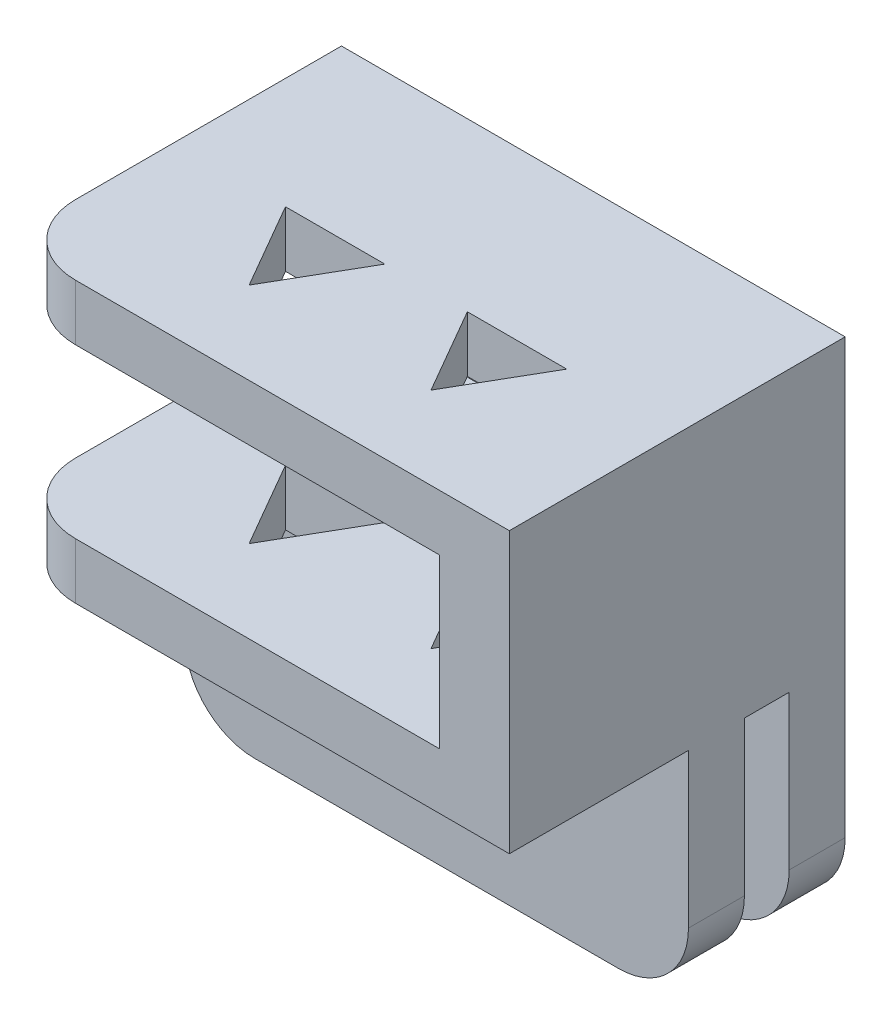
SolidWorks part; units mm, degrees
material "ABS"
ref_plane "Front Plane" through (0, 0, 0) normal (0, 0, 1) x (1, 0, 0)
ref_plane "Top Plane" through (0, 0, 0) normal (0, 1, 0) x (1, 0, 0)
ref_plane "Right Plane" through (0, 0, 0) normal (1, 0, 0) x (0, 0, -1)
sketch "Sketch1" plane through (0, 0, 0) normal (1, 0, 0) x (0, 0, -1)
  line L0 (6, -5) -> (6, -13)
  line L1 (-6, 5) -> (6, 5)
  line L2 (-6, 5) -> (-6, -5)
  line L3 (-6, -5) -> (0.4, -5)
  line L4 (6, 5) -> (6, -5)
  line L5 (-6, 5) -> (6, -5) construction
  line L6 (-6, -5) -> (6, 5) construction
  line L7 (6, -13) -> (4, -13)
  line L8 (4, -13) -> (4, -5)
  line L9 (2.4, -5) -> (2.4, -13)
  line L10 (2.4, -13) -> (0.4, -13)
  line L11 (0.4, -13) -> (0.4, -5)
  line L12 (2.4, -5) -> (4, -5)
  line L13 (0.4, -5) -> (2.4, -5) construction
  line L14 (4, -5) -> (6, -5) construction
  point P0 (0, 0)
  dimension "D1" = 2
  dimension "D2" = 2
  dimension "D3" = 8
  dimension "D4" = 8
  dimension "D5" = 1.6
  dimension "D6" = 10
  dimension "D7" = 12
extrude "Boss-Extrude1" add sketch "Sketch1" along normal mid plane 18
sketch "Sketch2" plane through (0, 0, 6) normal (0, 0, 1) x (1, 0, 0)
  line L0 (-6.5, 3) -> (-9, 3)
  line L1 (-6.5, 3) -> (6.5, 3)
  line L2 (-6.5, 3) -> (-6.5, -3) construction
  line L3 (-6.5, -3) -> (6.5, -3)
  line L4 (6.5, 3) -> (6.5, -3)
  line L5 (-6.5, 3) -> (6.5, -3) construction
  line L6 (-6.5, -3) -> (6.5, 3) construction
  line L7 (-9, 5) -> (-9, -5) construction
  line L8 (-6.5, -3) -> (-9, -3)
  line L9 (-9, 3) -> (-9, -3)
  point P0 (0, 0)
  dimension "D1" = 13
  dimension "D2" = 6
extrude "Cut-Extrude1" cut sketch "Sketch2" against normal through all
sketch "Sketch4" plane through (0, 5, 0) normal (0, 1, 0) x (1, 0, 0)
  line L1 (3.25, -3.05) -> (5.0254, 0.025)
  line L2 (5.0254, 0.025) -> (1.4746, 0.025)
  line L3 (1.4746, 0.025) -> (3.25, -3.05)
  line L4 (-1.4746, 0.025) -> (-5.0254, 0.025)
  line L5 (-5.0254, 0.025) -> (-3.25, -3.05)
  line L6 (-3.25, -3.05) -> (-1.4746, 0.025)
  circle A0 centre (3.25, -1) radius 1.025 construction
  circle A1 centre (3.25, -1) radius 1.025 construction
  circle A2 centre (-3.25, -1) radius 1.025 construction
  circle A3 centre (-3.25, -1) radius 1.025 construction
extrude "Cut-Extrude2" cut sketch "Sketch4" against normal through all
fillet "Fillet1" radius 2.5 6 edges at (9, -13, -1.4) (9, -13, -5) (-9, -13, -5) (-9, -13, -1.4) (-9, 4, 6) (-9, -4, 6)
